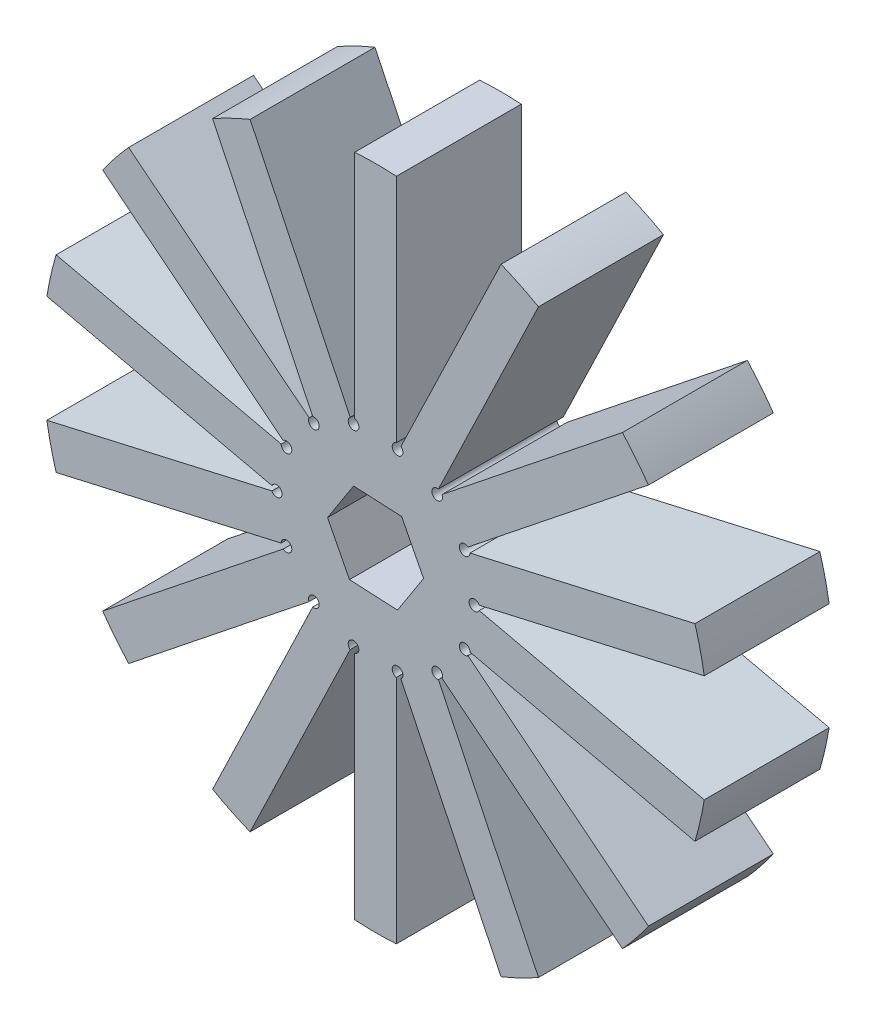
SolidWorks part; units mm, degrees
ref_plane "Front Plane" through (0, 0, 0) normal (0, 0, 1) x (1, 0, 0)
ref_plane "Top Plane" through (0, 0, 0) normal (0, 1, 0) x (1, 0, 0)
ref_plane "Right Plane" through (0, 0, 0) normal (1, 0, 0) x (0, 0, -1)
sketch "Sketch1" plane through (0, 0, 0) normal (0, 0, 1) x (1, 0, 0)
  line L0 (-34.0287, 20.0475) -> (-68.4455, 27.9029)
  line L3 (-32.6157, 26.2383) -> (-67.0325, 34.0937)
  line L4 (-27.7976, 32.2799) -> (-43.1145, 64.0859)
  line L7 (-22.0765, 35.0351) -> (-37.3934, 66.841)
  line L8 (-21.3877, 70.4942) -> (-21.3877, 35.1923)
  line L9 (-37.3934, -27.4526) -> (-22.0765, 4.3534)
  line L10 (19.5248, 53.8498) -> (-8.0754, 31.8394)
  line L11 (-67.0325, 5.2948) -> (-32.6157, 13.1502)
  line L12 (32.0202, 11.4856) -> (-2.3966, 19.341)
  line L13 (-59.9093, 48.8852) -> (-32.3091, 26.8748)
  line L14 (6.6892, -24.6974) -> (-8.6277, 7.1085)
  line L15 (-15.0377, 70.4942) -> (-15.0377, 35.1923)
  line L16 (-43.1145, -24.6974) -> (-27.7976, 7.1085)
  line L17 (23.484, 48.8852) -> (-4.1162, 26.8748)
  line L18 (-68.4455, 11.4856) -> (-34.0287, 19.341)
  line L19 (30.6072, 5.2948) -> (-3.8097, 13.1502)
  line L20 (-55.9501, 53.8498) -> (-28.35, 31.8394)
  line L21 (0.9681, -27.4526) -> (-14.3489, 4.3534)
  line L23 (-14.3489, 35.0351) -> (0.9681, 66.841)
  line L26 (-8.6277, 32.2799) -> (6.6892, 64.0859)
  line L27 (-3.8097, 26.2383) -> (30.6072, 34.0937)
  line L30 (-2.3966, 20.0475) -> (32.0202, 27.9029)
  line L31 (-4.1162, 12.5136) -> (23.484, -9.4967)
  line L34 (-8.0754, 7.549) -> (19.5248, -14.4614)
  line L35 (-15.0377, 4.1961) -> (-15.0377, -31.1058)
  line L38 (-21.3877, 4.1961) -> (-21.3877, -31.1058)
  line L39 (-28.35, 7.549) -> (-55.9501, -14.4614)
  line L42 (-32.3091, 12.5136) -> (-59.9093, -9.4967)
  line L43 (-18.2127, 19.6942) -> (-21.5688, 34.3986) construction
  line L44 (-14.8666, 13.1699) -> (-10.8894, 19.3298)
  line L45 (-10.8894, 19.3298) -> (-14.2354, 25.8542)
  line L46 (-14.2354, 25.8542) -> (-21.5587, 26.2186)
  line L47 (-21.5587, 26.2186) -> (-25.536, 20.0586)
  line L48 (-25.536, 20.0586) -> (-22.1899, 13.5343)
  line L49 (-22.1899, 13.5343) -> (-14.8666, 13.1699)
  arc A0 (-55.8725, 53.7879) -> (-59.8316, 48.8233) centre (-18.2127, 19.6942) ccw
  arc A1 (-66.9357, 34.0716) -> (-68.3487, 27.8808) centre (-18.2127, 19.6942) ccw
  arc A2 (-68.3487, 11.5077) -> (-66.9357, 5.3169) centre (-18.2127, 19.6942) ccw
  arc A3 (-59.8316, -9.4348) -> (-55.8725, -14.3995) centre (-18.2127, 19.6942) ccw
  arc A4 (-43.0714, -24.6079) -> (-37.3503, -27.3631) centre (-18.2127, 19.6942) ccw
  arc A5 (-21.3877, -31.0065) -> (-15.0377, -31.0065) centre (-18.2127, 19.6942) ccw
  arc A6 (0.925, -27.3631) -> (6.6461, -24.6079) centre (-18.2127, 19.6942) ccw
  arc A7 (19.4471, -14.3995) -> (23.4063, -9.4348) centre (-18.2127, 19.6942) ccw
  arc A8 (30.5103, 5.3169) -> (31.9234, 11.5077) centre (-18.2127, 19.6942) ccw
  arc A9 (31.9234, 27.8808) -> (30.5103, 34.0716) centre (-18.2127, 19.6942) ccw
  arc A10 (23.4063, 48.8233) -> (19.4471, 53.7879) centre (-18.2127, 19.6942) ccw
  arc A11 (6.6461, 63.9964) -> (0.925, 66.7515) centre (-18.2127, 19.6942) ccw
  arc A12 (-15.0377, 70.3949) -> (-21.3877, 70.3949) centre (-18.2127, 19.6942) ccw
  arc A13 (-37.3503, 66.7515) -> (-43.0714, 63.9964) centre (-18.2127, 19.6942) ccw
  circle A14 centre (-18.2127, 19.6942) radius 6.35 construction
  arc A15 (-22.0765, 35.0351) -> (-21.3877, 35.1923) centre (-21.5688, 34.3986) ccw
  arc A16 (-15.0377, 35.1923) -> (-14.3489, 35.0351) centre (-14.8565, 34.3986) ccw
  arc A17 (-8.6277, 32.2799) -> (-8.0754, 31.8394) centre (-8.8089, 31.4862) ccw
  arc A18 (-4.1162, 26.8748) -> (-3.8097, 26.2383) centre (-4.6238, 26.2383) ccw
  arc A19 (-2.3966, 20.0475) -> (-2.3966, 19.341) centre (-3.1302, 19.6942) ccw
  arc A20 (-3.8097, 13.1502) -> (-4.1162, 12.5136) centre (-4.6238, 13.1502) ccw
  arc A21 (-8.0754, 7.549) -> (-8.6277, 7.1085) centre (-8.8089, 7.9023) ccw
  arc A22 (-14.3489, 4.3534) -> (-15.0377, 4.1961) centre (-14.8565, 4.9899) ccw
  arc A23 (-21.3877, 4.1961) -> (-22.0765, 4.3534) centre (-21.5688, 4.9899) ccw
  arc A24 (-27.7976, 7.1085) -> (-28.35, 7.549) centre (-27.6164, 7.9023) ccw
  arc A25 (-32.3091, 12.5136) -> (-32.6157, 13.1502) centre (-31.8015, 13.1502) ccw
  arc A26 (-34.0287, 19.341) -> (-34.0287, 20.0475) centre (-33.2951, 19.6942) ccw
  arc A27 (-32.6157, 26.2383) -> (-32.3091, 26.8748) centre (-31.8015, 26.2383) ccw
  arc A28 (-28.35, 31.8394) -> (-27.7976, 32.2799) centre (-27.6164, 31.4862) ccw
  point P73 (-22.0765, 35.0351)
  point P81 (-21.3877, 35.1923)
  dimension "D1" = 101.6
  dimension "D3" = 15.0825
  dimension "D2" = 14
extrude "Boss-Extrude1" add sketch "Sketch1" along normal blind 19.05 contours A28 L20 A0 L13 A27 L3 A1 L0 A26 L18 A2 L11 A25 L42 A3 L39 A24 L16 A4 L9 A23 L38 A5 L35 A22 L21 A6 L14 A21 L34 A7 L31 A20 L19 A8 L12 A19 L30 A9 L27 A18 L17 A10 L10 A17 L26 A11 L23 A16 L15 A12
